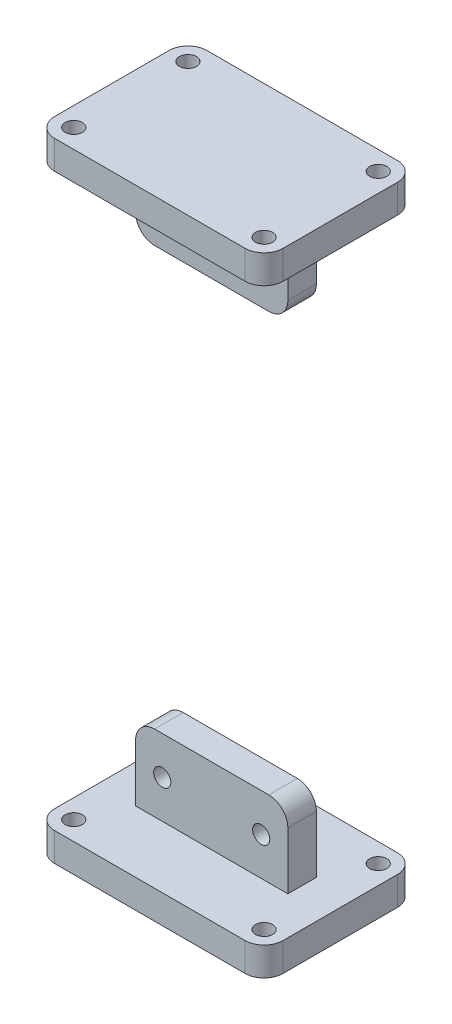
SolidWorks part; units mm, degrees
ref_plane "Front Plane" through (0, 0, 0) normal (0, 0, 1) x (1, 0, 0)
ref_plane "Top Plane" through (0, 0, 0) normal (0, 1, 0) x (1, 0, 0)
ref_plane "Right Plane" through (0, 0, 0) normal (1, 0, 0) x (0, 0, -1)
sketch "Sketch1" plane through (0, 0, 0) normal (0, 1, 0) x (1, 0, 0)
  line L1 (60, -40) -> (-60, -40)
  line L2 (60, -40) -> (60, 40)
  line L3 (60, 40) -> (-60, 40)
  line L4 (-60, -40) -> (-60, 40)
  line L5 (60, -40) -> (-60, 40) construction
  line L6 (60, 40) -> (-60, -40) construction
  point P0 (0, 0)
  dimension "D1" = 120
  dimension "D2" = 80
extrude "Boss-Extrude1" add sketch "Sketch1" along normal blind 15
fillet "Fillet1" radius 10 1 edges at (60, 7.5, 40)
fillet "Fillet2" radius 10 1 edges at (-60, 7.5, 40)
fillet "Fillet3" radius 10 1 edges at (-60, 7.5, -40)
fillet "Fillet4" radius 10 1 edges at (60, 7.5, -40)
sketch "Sketch2" plane through (0, 0, 0) normal (0, 1, 0) x (1, 0, 0)
  line L0 (0, 0) -> (0, -43.5282) construction
  line L1 (0, -43.5282) -> (0, 43.3871) construction
  line L2 (0, 0) -> (84.827, 0) construction
  line L3 (84.827, 0) -> (-92.4462, 0) construction
  circle A0 centre (-50, 30) radius 4.5
  circle A1 centre (-50, -30) radius 4.5
  circle A2 centre (50, -30) radius 4.5
  circle A3 centre (50, 30) radius 4.5
  dimension "D1" = 9
extrude "Cut-Extrude1" cut sketch "Sketch2" against normal through all both and the other way through all
sketch "Sketch4" plane through (0, 0, 0) normal (0, 1, 0) x (1, 0, 0)
  line L1 (40, -7.5) -> (-40, -7.5)
  line L2 (40, -7.5) -> (40, 7.5)
  line L3 (40, 7.5) -> (-40, 7.5)
  line L4 (-40, -7.5) -> (-40, 7.5)
  line L5 (40, -7.5) -> (-40, 7.5) construction
  line L6 (40, 7.5) -> (-40, -7.5) construction
  point P0 (0, 0)
  dimension "D1" = 80
  dimension "D2" = 15
extrude "Boss-Extrude2" add sketch "Sketch4" against normal blind 40
fillet "Fillet5" radius 10 1 edges at (-40, -40, 0)
fillet "Fillet6" radius 10 1 edges at (40, -40, 0)
sketch "Sketch5" plane through (0, 0, 0) normal (0, 0, 1) x (1, 0, 0)
  circle A0 centre (-26, -20) radius 4.5
  dimension "D3" = 9
extrude "Cut-Extrude2" cut sketch "Sketch5" against normal through all both and the other way through all
sketch "Sketch6" plane through (0, 0, 0) normal (0, 0, 1) x (1, 0, 0)
  circle A0 centre (26, -20) radius 4.5
extrude "Cut-Extrude3" cut sketch "Sketch6" against normal through all both and the other way through all
move or copy body "Body-Move/Copy3" bodies to move or copy 105 copy yes number of copies 1 rotation origin (0, -150, 0) rotation axis (1, 0, 0) rotation angle 180
